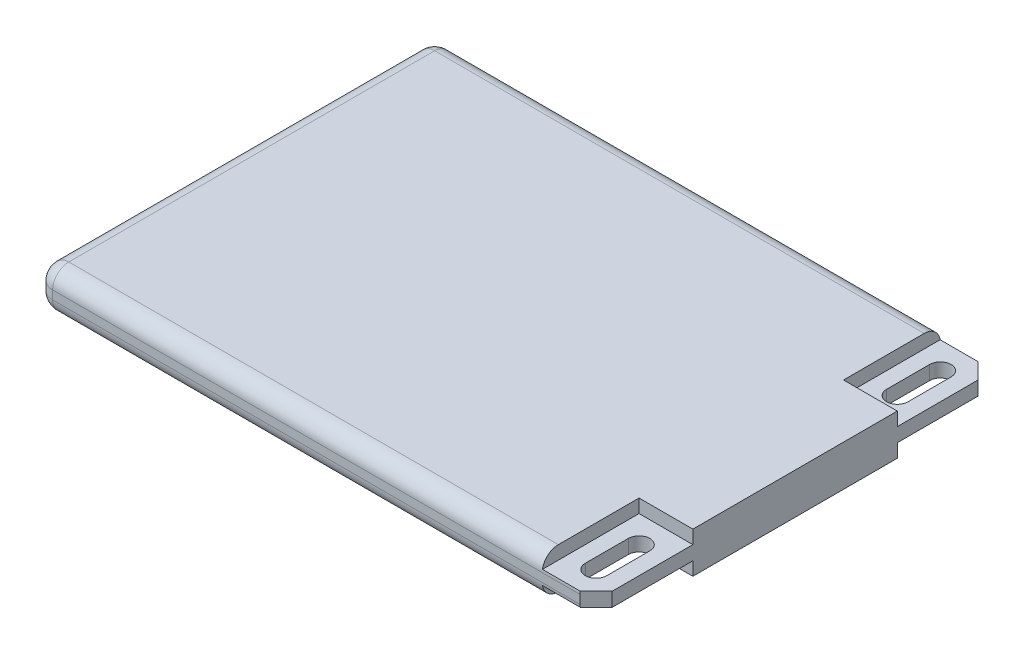
SolidWorks part; units mm, degrees
material "Plain Carbon Steel"
ref_plane "Front Plane" through (0, 0, 0) normal (0, 0, 1) x (1, 0, 0)
ref_plane "Top Plane" through (0, 0, 0) normal (0, 1, 0) x (1, 0, 0)
ref_plane "Right Plane" through (0, 0, 0) normal (1, 0, 0) x (0, 0, -1)
sketch "Sketch1" plane through (0, 0, 0) normal (0, 1, 0) x (1, 0, 0)
  line L1 (-26, -18.5) -> (26, -18.5)
  line L2 (-26, -18.5) -> (-26, 18.5)
  line L3 (-26, 18.5) -> (26, 18.5)
  line L4 (26, -18.5) -> (26, 18.5)
  line L5 (-26, -18.5) -> (26, 18.5) construction
  line L6 (-26, 18.5) -> (26, -18.5) construction
  point P0 (0, 0)
  dimension "D1" = 52
  dimension "D2" = 37
extrude "Boss-Extrude1" add sketch "Sketch1" along normal mid plane 3.8
sketch "Sketch2" plane through (0, 1.9, 0) normal (0, 1, 0) x (1, 0, 0)
  line L0 (-26, 0) -> (30.1491, 0) construction
  line L1 (26, 18.5) -> (21, 18.5)
  line L2 (26, 18.5) -> (26, 9.5)
  line L3 (26, 9.5) -> (21, 9.5)
  line L4 (21, 18.5) -> (21, 9.5)
  line L5 (-26, 18.5) -> (-26, -18.5) construction
  line L6 (26, -9.5) -> (21, -9.5)
  line L7 (26, -18.5) -> (26, -9.5)
  line L8 (26, -18.5) -> (21, -18.5)
  line L9 (21, -18.5) -> (21, -9.5)
  dimension "D1" = 9
  dimension "D2" = 5
extrude "Cut-Extrude1" cut sketch "Sketch2" against normal blind 1.25
mirror "Mirror1" about plane through (0, 0, 0) normal (0, 1, 0) of "Cut-Extrude1"
sketch "Sketch3" plane through (0, 0.65, 0) normal (0, 1, 0) x (1, 0, 0)
  line L0 (26, 18.5) -> (21, 18.5) construction
  line L1 (-26, 0) -> (26, 0) construction
  line L2 (22.5, 12) -> (22.5, 16)
  line L4 (24.5, 12) -> (24.5, 16)
  line L5 (22.5, 12) -> (24.5, 16) construction
  line L6 (22.5, 16) -> (24.5, 12) construction
  line L7 (26, 9.5) -> (26, 18.5) construction
  line L8 (-26, 18.5) -> (-26, -18.5) construction
  line L9 (26, -9.5) -> (26, 9.5) construction
  line L10 (22.5, -12) -> (22.5, -16)
  line L11 (24.5, -12) -> (24.5, -16)
  arc A0 (22.5, 16) -> (24.5, 16) centre (23.5, 16) cw
  arc A1 (24.5, 12) -> (22.5, 12) centre (23.5, 12) cw
  arc A2 (22.5, -16) -> (24.5, -16) centre (23.5, -16) ccw
  arc A3 (24.5, -12) -> (22.5, -12) centre (23.5, -12) ccw
  point P0 (23.5, 14)
  point P7 (23.5, 18.5)
  point P10 (26, 14)
extrude "Cut-Extrude2" cut sketch "Sketch3" against normal through all
chamfer "Chamfer1" distance 1.5 angle 45 2 edges at (26, 0, 18.5) (26, 0, -18.5)
fillet "Fillet2" radius 1.5 8 edges at (-2.5, -1.9, -18.5) (-26, 0, -18.5) (-26, 0, 18.5) (-26, -1.9, 0) (-2.5, -1.9, 18.5) (-2.5, 1.9, 18.5) (-26, 1.9, 0) (-2.5, 1.9, -18.5)
